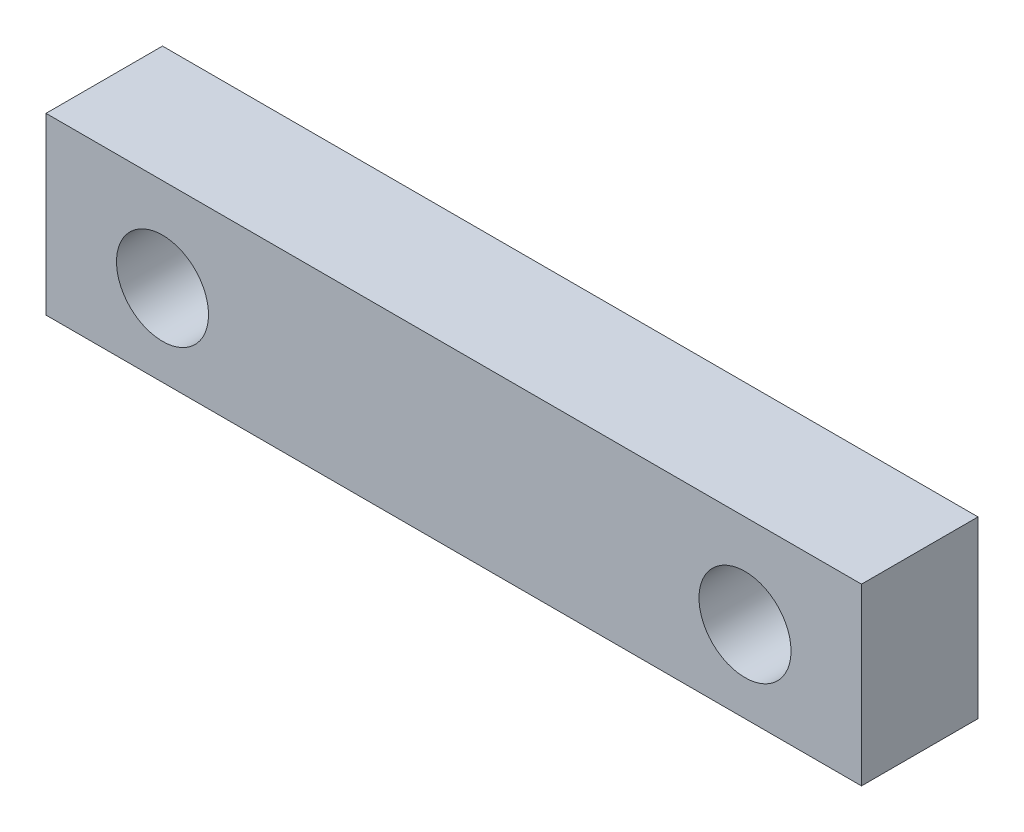
SolidWorks part; units mm, degrees
ref_plane "Спереди" through (0, 0, 0) normal (0, 0, 1) x (1, 0, 0)
ref_plane "Сверху" through (0, 0, 0) normal (0, 1, 0) x (1, 0, 0)
ref_plane "Справа" through (0, 0, 0) normal (1, 0, 0) x (0, 0, -1)
sketch "Эскиз1" plane through (0, 0, 0) normal (0, 0, 1) x (1, 0, 0)
  line L2 (-102.3538, 58.0057) -> (-146.8038, 58.0057) construction
  line L5 (-102.3538, 58.0057) -> (-146.8038, 58.0057)
  line L11 (-146.8038, 58.0057) -> (-146.8038, 48.4807)
  line L12 (-146.8038, 48.4807) -> (-102.3538, 48.4807)
  line L13 (-102.3538, 48.4807) -> (-102.3538, 58.0057)
  circle A0 centre (-108.7038, 52.9257) radius 2.5083 construction
  circle A1 centre (-140.4538, 52.9257) radius 2.5083 construction
  circle A2 centre (-108.7038, 52.9257) radius 2.5083
  circle A3 centre (-140.4538, 52.9257) radius 2.5082
  dimension "D1" = 9.525
extrude "Бобышка-Вытянуть1" add sketch "Эскиз1" along normal blind 6.35
